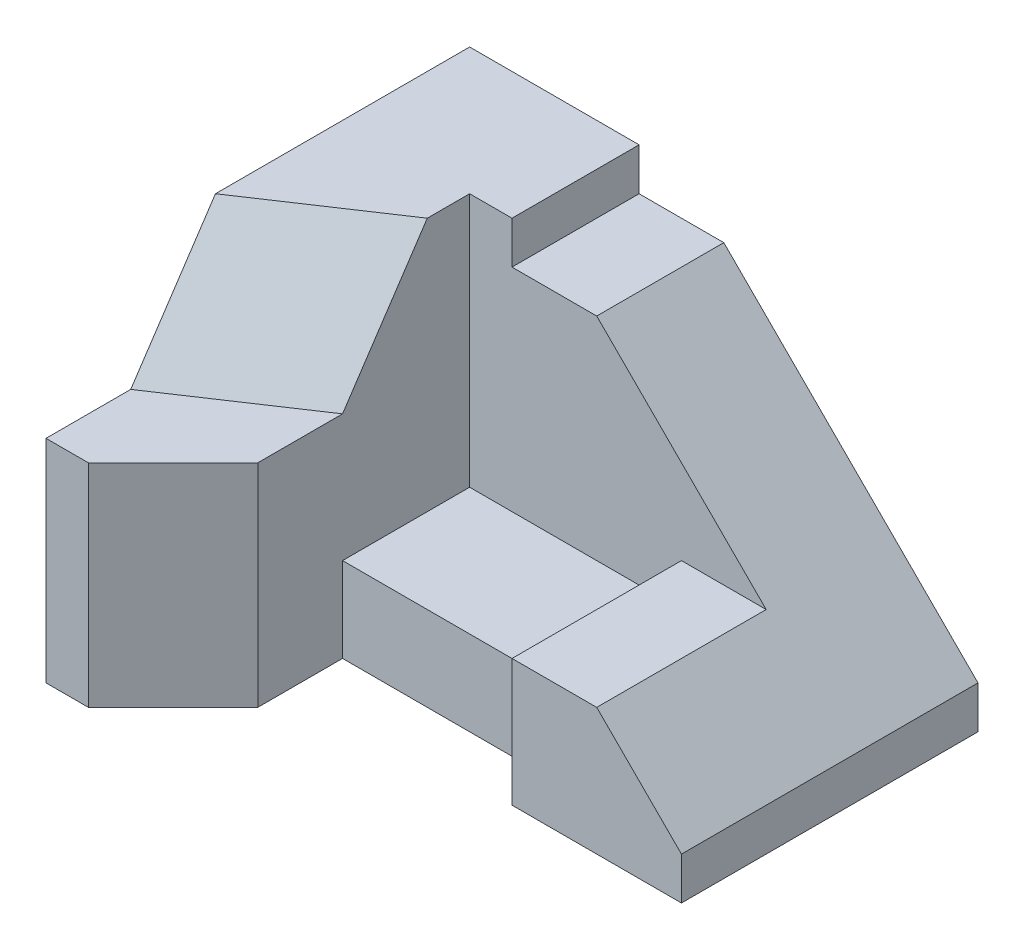
SolidWorks part; units mm, degrees
ref_plane "Front Plane" through (0, 0, 0) normal (0, 0, 1) x (1, 0, 0)
ref_plane "Top Plane" through (0, 0, 0) normal (0, 1, 0) x (1, 0, 0)
ref_plane "Right Plane" through (0, 0, 0) normal (1, 0, 0) x (0, 0, -1)
sketch "Sketch1" plane through (0, 0, 0) normal (0, 1, 0) x (1, 0, 0)
  line L0 (0, 0) -> (0, 60)
  line L1 (0, 60) -> (40, 60)
  line L2 (40, 60) -> (40, 30)
  line L3 (40, 30) -> (30, 30)
  line L4 (30, 30) -> (30, 20)
  line L5 (30, 20) -> (0, 0)
  dimension "D1" = 60
  dimension "D2" = 40
  dimension "D3" = 30
  dimension "D4" = 10
  dimension "D5" = 10
extrude "Boss-Extrude1" add sketch "Sketch1" along normal blind 80
sketch "Sketch2" plane through (0, 0, 0) normal (-1, 0, 0) x (0, 0, 1)
  line L0 (0, 80) -> (20, 50)
  line L1 (20, 50) -> (40, 50)
  line L2 (40, 50) -> (40, 0)
  line L3 (40, 0) -> (0, 0)
  line L4 (0, 0) -> (-60, 0)
  line L5 (-60, 80) -> (0, 80)
  line L6 (20, 50) -> (40, 50)
  line L7 (0, 80) -> (0, 0)
  line L8 (-60, 0) -> (0, 0)
  line L9 (0, 0) -> (0, 80)
  line L10 (0, 80) -> (-60, 80)
  line L11 (-60, 80) -> (-60, 0)
  line L12 (-60, 0) -> (0, 0)
  line L14 (0, 80) -> (-60, 80)
  line L15 (-60, 80) -> (-60, 0)
  line M5 (-60, 0) -> (0, 0)
  line M6 (0, 0) -> (0, 80)
  line M7 (0, 80) -> (-60, 80)
  line M8 (-60, 80) -> (-60, 0)
  dimension "D1" = 40
  dimension "D2" = 50
  dimension "D3" = 20
  dimension "D4" = 0
extrude "Boss-Extrude6" add sketch "Sketch2" against normal blind 10 contours M8 M5 M6 M7 | L3 L2 L1 L0 M6
sketch "Sketch7" plane through (0, 50, 0) normal (0, 1, 0) x (1, 0, 0)
  line L0 (0, -20) -> (30, 0)
  dimension "D1" = 30
  dimension "D2" = 20
ref_plane "Plane2" through (18.8235, 18.8235, 28.2353) normal (0.4851, 0.4851, 0.7276) x (0.8745, -0.2691, -0.4036)
sketch "Sketch8" plane through (18.8235, 18.8235, 28.2353) normal (0.4851, 0.4851, 0.7276) x (0.8745, -0.2691, -0.4036)
  line L0 (-21.5255, 30.5085) -> (12.7808, 41.6025)
  line L1 (12.7808, 41.6025) -> (12.7808, 77.658)
  line L2 (12.7808, 77.658) -> (-21.5255, 66.564)
  line L3 (-21.5255, 66.564) -> (-21.5255, 30.5085)
extrude "Cut-Extrude3" cut sketch "Sketch8" along normal blind 149
ref_plane "Plane3" through (28.525, 28.525, 42.7874) normal (0.4851, 0.4851, 0.7276) x (0.8745, -0.2691, -0.4036)
sketch "Sketch10" plane through (18.8235, 18.8235, 28.2353) normal (0.4851, 0.4851, 0.7276) x (0.8745, -0.2691, -0.4036)
  line L0 (-21.5255, 30.5085) -> (12.7808, 41.6025)
  line L1 (12.7808, 41.6025) -> (12.7808, 77.658)
  line L2 (12.7808, 77.658) -> (-21.5255, 66.564)
  line L3 (-21.5255, 66.564) -> (-21.5255, 30.5085)
extrude "Boss-Extrude7" add sketch "Sketch10" against normal blind 20
sketch "Sketch11" plane through (0, 0, 0) normal (-1, 0, 0) x (0, 0, 1)
  line L1 (-60, 80) -> (40, 80)
  line L2 (-60, 80) -> (-60, 0)
  line L3 (-60, 0) -> (40, 0)
  line L4 (40, 80) -> (40, 0)
extrude "Cut-Extrude4" cut sketch "Sketch11" along normal blind 20
sketch "Sketch12" plane through (0, 50, 0) normal (0, 1, 0) x (1, 0, 0)
  line L0 (0, -20) -> (10, -13.3333)
  line L1 (10, -13.3333) -> (10, -40)
  line L2 (10, -40) -> (0, -40)
  line L3 (0, -40) -> (0, -20)
extrude "Cut-Extrude5" cut sketch "Sketch12" along normal blind 20
sketch "Sketch14" plane through (0, 0, 0) normal (0.5547, 0, 0.8321) x (0.8321, 0, -0.5547)
  line L0 (12.0185, 0) -> (12.0185, 40.7692) construction
  line L1 (36.0555, 0) -> (12.0185, 0)
  line L2 (36.0555, 0) -> (36.0555, 50)
  line L3 (36.0555, 50) -> (12.0185, 50)
  line L4 (12.0185, 0) -> (12.0185, 50)
  dimension "D1" = 50
extrude "Cut-Extrude6" cut sketch "Sketch14" along normal blind 29
sketch "Sketch15" plane through (10, 0, 0) normal (1, 0, 0) x (0, 0, -1)
  line L0 (6.6667, 50) -> (6.6667, 40.7692) construction
  line L1 (-40, 0) -> (6.6667, 0)
  line L2 (-40, 0) -> (-40, 50)
  line L3 (-40, 50) -> (6.6667, 50)
  line L4 (6.6667, 0) -> (6.6667, 50)
  dimension "D1" = 50
extrude "Cut-Extrude7" cut sketch "Sketch15" along normal blind 29
ref_plane "Plane4" through (0, 70, 0) normal (0, 1, 0) x (1, 0, 0)
sketch "Sketch16" plane through (0, 70, 0) normal (0, 1, 0) x (1, 0, 0)
  line L1 (40, 60) -> (60, 60)
  line L2 (40, 60) -> (40, 30)
  line L3 (40, 30) -> (60, 30)
  line L4 (60, 60) -> (60, 30)
  dimension "D1" = 20
  dimension "D2" = 30
  dimension "D3" = 0
extrude "Boss-Extrude8" add sketch "Sketch16" against normal blind 70
sketch "Sketch17" plane through (0, 0, -60) normal (0, 0, -1) x (-1, 0, 0)
  line L0 (-60, 70) -> (-100, 10)
  line L1 (-100, 10) -> (-80, 10)
  line L2 (-80, 10) -> (-80, 0)
  line L3 (-80, 0) -> (-60, 0)
  line L4 (-60, 0) -> (-60, 70)
  line L5 (-60, 70) -> (-60.1567, 70.3189)
  line M5 (-60, 70) -> (-60, 0)
  dimension "D1" = 20
  dimension "D2" = 10
  dimension "D3" = 20
extrude "Boss-Extrude10" add sketch "Sketch17" against normal blind 30 contours L2 L3 L0 L1 M5
sketch "Sketch21" plane through (0, 0, -30) normal (0, 0, 1) x (1, 0, 0)
  line L1 (60, 70) -> (103.2058, 70)
  line L2 (60, 70) -> (60, -4.0528)
  line L3 (60, -4.0528) -> (103.2058, -4.0528)
  line L4 (103.2058, 70) -> (103.2058, -4.0528)
  dimension "D1" = 43.2058
  dimension "D2" = 74.0528
extrude "Cut-Extrude9" cut sketch "Sketch21" against normal blind 30
sketch "Sketch22" plane through (0, 0, -30) normal (0, 0, 1) x (1, 0, 0)
  line L0 (60, 0) -> (60, 20)
  line L4 (60, 20) -> (60, 70)
  line L6 (30, 0) -> (60, 0)
  line L7 (30, 0) -> (30, 20)
  line L8 (30, 20) -> (60, 20)
  line M1 (30, 0) -> (60, 0)
  line M2 (60, 0) -> (60, 70)
  line M6 (30, 80) -> (30, 0)
  dimension "D1" = 20
extrude "Cut-Extrude10" cut sketch "Sketch22" against normal blind 30 contours L8 M6 M1 M2
sketch "Sketch23" plane through (0, 0, -30) normal (0, 0, 1) x (1, 0, 0)
  line L0 (60, 70) -> (100, 30)
  line L1 (100, 30) -> (80, 30)
  line L2 (80, 30) -> (80, 20)
  line L3 (80, 20) -> (60, 20)
  line L4 (60, 20) -> (60, 70)
  dimension "D1" = 40
  dimension "D2" = 40
  dimension "D3" = 10
  dimension "D4" = 20
extrude "Boss-Extrude11" add sketch "Sketch23" against normal blind 30
sketch "Sketch24" plane through (0, 0, -30) normal (0, 0, 1) x (1, 0, 0)
  line L0 (100, 30) -> (120, 10)
  line L1 (120, 10) -> (120, 0)
  line L2 (120, 0) -> (80, 0)
  line L3 (80, 0) -> (80, 30)
  line L4 (80, 30) -> (100, 30)
  dimension "D1" = 10
  dimension "D2" = 40
extrude "Boss-Extrude12" add sketch "Sketch24" against normal blind 30 and the other way blind 40
sketch "Sketch25" plane through (0, 0, -60) normal (0, 0, -1) x (-1, 0, 0)
  line L1 (-80, 20) -> (-30, 20)
  line L2 (-80, 20) -> (-80, 0)
  line L3 (-80, 0) -> (-30, 0)
  line L4 (-30, 20) -> (-30, 0)
extrude "Boss-Extrude13" add sketch "Sketch25" against normal blind 60
sketch "Sketch28" plane through (0, 0, 0) normal (0, -1, 0) x (-1, 0, 0)
  line L0 (-30, 20) -> (-10, 6.6667)
  line L1 (-30, 20) -> (-30, 0)
  line L2 (-30, 0) -> (-30, -20)
  line L3 (-30, -20) -> (-10, -40)
  line L4 (-10, -40) -> (0, -40)
  line L5 (0, -40) -> (0, -20)
  line L6 (0, -20) -> (-30, 20)
  line L7 (-10, 6.6667) -> (-10, -6.6667)
  line L8 (-10, 6.6667) -> (-10, -40) construction
  line M6 (-30, 0) -> (-30, 20)
  line M7 (-30, 20) -> (-10, 6.6667)
  line M8 (-10, 6.6667) -> (-10, -40)
  dimension "D1" = 20
  dimension "D2" = 20
  dimension "D3" = 20
extrude "Boss-Extrude16" add sketch "Sketch28" against normal blind 50 contours L6 M8 M7 | L6 L2 L3 M8 M6
sketch "Sketch29" plane through (30, 0, 0) normal (1, 0, 0) x (0, 0, -1)
  line L0 (0, 50) -> (20, 50)
  line L1 (20, 50) -> (20, 80)
  line L2 (20, 80) -> (0, 50)
extrude "Boss-Extrude17" add sketch "Sketch29" against normal blind 20
